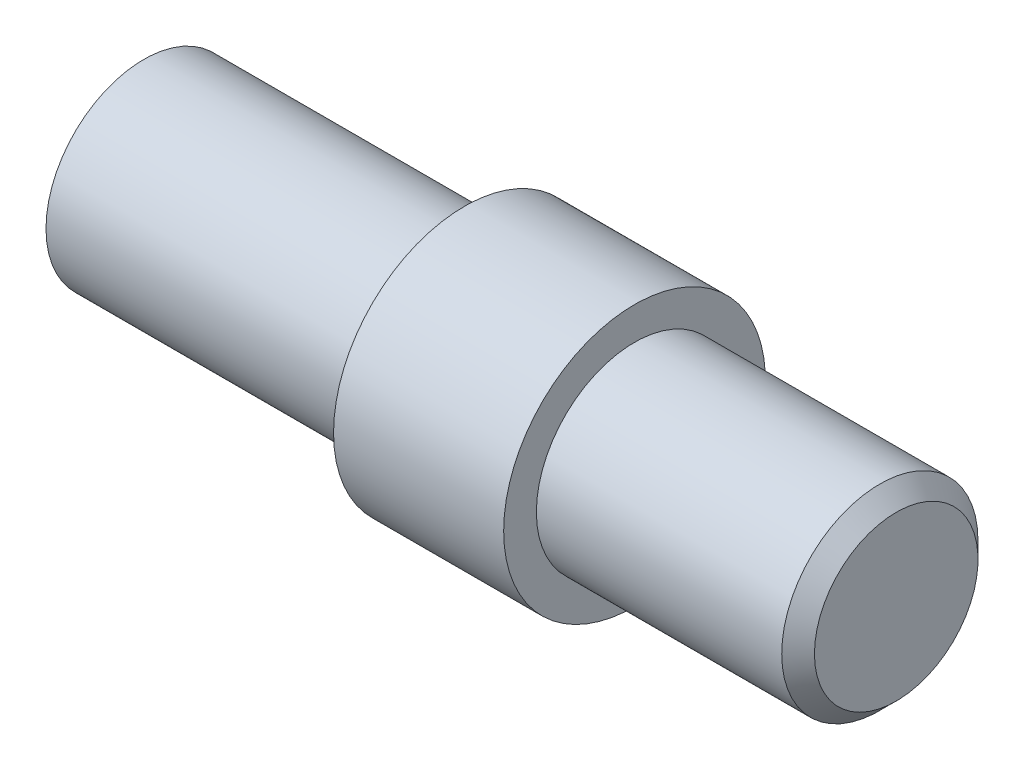
SolidWorks part; units mm, degrees
ref_plane "Front Plane" through (0, 0, 0) normal (0, 0, 1) x (1, 0, 0)
ref_plane "Top Plane" through (0, 0, 0) normal (0, 1, 0) x (1, 0, 0)
ref_plane "Right Plane" through (0, 0, 0) normal (1, 0, 0) x (0, 0, -1)
sketch "Sketch1" plane through (0, 0, 0) normal (0, 0, 1) x (1, 0, 0)
  line L0 (0, 0) -> (23, 0)
  line L1 (23, 0) -> (23, 3)
  line L2 (23, 3) -> (15, 3)
  line L3 (15, 3) -> (15, 4)
  line L4 (15, 4) -> (9.8, 4)
  line L5 (9.8, 4) -> (9.8, 2.99)
  line L6 (9.8, 2.99) -> (0, 2.99)
  line L7 (0, 2.99) -> (0, 0)
  dimension "D1" = 2.99
  dimension "D2" = 3
  dimension "D3" = 9.8
  dimension "D4" = 5.2
  dimension "D5" = 8
  dimension "D6" = 4
revolve "Revolve1" add sketch "Sketch1" angle 360 about L0
chamfer "Chamfer1" distance 0.5 angle 45 1 edges at (23, 0, 3)
hole_wizard "Tap Drill for M3x0.5 Tap1" positions "Sketch3" profile "Sketch2" hole size "M3x0.5" standard "ANSI Metric"
sketch "Sketch3" plane through (0, 0, 0) normal (-1, 0, 0) x (0, 0, 1)
  point P0 (0, 0)
sketch "Sketch2" plane through (0, 0, 0) normal (0, 1, 0) x (0, 0, 1)
  line L0 (0, 0) -> (0, 6.7511)
  line L1 (0, 6.7511) -> (1.25, 6)
  line L2 (1.25, 6) -> (1.25, 0)
  line L5 (1.25, 0) -> (0, 0)
  line L10 (0, 6.7511) -> (-1.25, 6) construction
  line L11 (0, -6.35) -> (0, 107.95) construction
  dimension "Hole Dia." = 2.5
  dimension "Hole Depth" = 6
  dimension "Drill Angle" = 118
